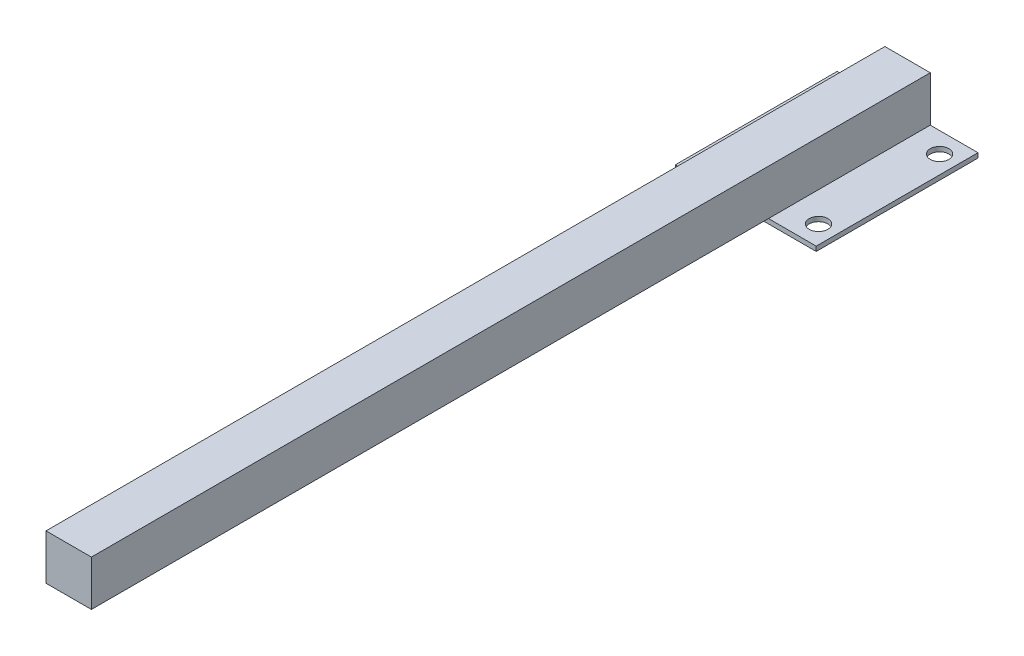
SolidWorks part; units mm, degrees
ref_plane "Front Plane" through (0, 0, 0) normal (0, 0, 1) x (1, 0, 0)
ref_plane "Top Plane" through (0, 0, 0) normal (0, 1, 0) x (1, 0, 0)
ref_plane "Right Plane" through (0, 0, 0) normal (1, 0, 0) x (0, 0, -1)
sketch "Sketch1" plane through (0, 0, 0) normal (0, 1, 0) x (1, 0, 0)
  line L0 (0, -34.75) -> (0, 34.75) construction
  line L1 (-30.25, 34.75) -> (30.25, 34.75)
  line L2 (-30.25, 34.75) -> (-30.25, -34.75)
  line L3 (-30.25, -34.75) -> (30.25, -34.75)
  line L4 (30.25, 34.75) -> (30.25, -34.75)
  line L5 (-30.25, 0) -> (30.25, 0) construction
  circle A0 centre (-22.5, 26) radius 4
  circle A1 centre (22.5, 26) radius 4
  circle A2 centre (-22.5, -26) radius 4
  circle A3 centre (22.5, -26) radius 4
  point P0 (0, 0)
  point P9 (0, 0)
  point P12 (0, 0)
  dimension "D3" = 8
  dimension "D4" = 22.5
  dimension "D5" = 26
  dimension "D1" = 60.5
  dimension "D2" = 69.5
extrude "Boss-Extrude1" add sketch "Sketch1" along normal blind 2
sketch "Sketch2" plane through (0, 0, 0) normal (0, 0, 1) x (1, 0, 0)
  line L0 (-30.25, 2) -> (30.25, 2) construction
  line L1 (-9.75, 2) -> (9.75, 2)
  line L2 (-9.75, 2) -> (-9.75, 21.5)
  line L3 (-9.75, 21.5) -> (9.75, 21.5)
  line L4 (9.75, 2) -> (9.75, 21.5)
  dimension "D1" = 19.5
  dimension "D2" = 19.5
  dimension "D3" = 9.75
extrude "Boss-Extrude2" add sketch "Sketch2" along normal blind 325.596 and the other way up to surface (34.75 mm away) other way up to face at (0, 1, -34.75)
